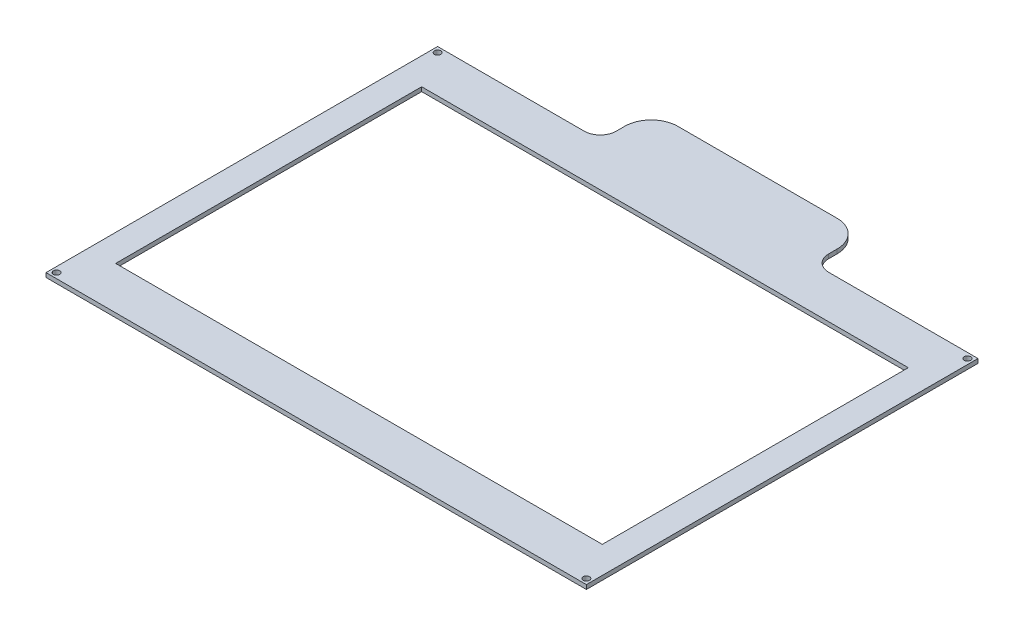
SolidWorks part; units mm, degrees
ref_plane "Front Plane" through (0, 0, 0) normal (0, 0, 1) x (1, 0, 0)
ref_plane "Top Plane" through (0, 0, 0) normal (0, 1, 0) x (1, 0, 0)
ref_plane "Right Plane" through (0, 0, 0) normal (1, 0, 0) x (0, 0, -1)
sketch "Sketch3" plane through (0, 0, 0) normal (0, 1, 0) x (1, 0, 0)
  line L0 (-127.15, 80.1414) -> (-58.1228, 80.1414)
  line L1 (-50.6228, 91.6414) -> (-50.6228, 87.6414)
  line L2 (-38.1228, 104.1414) -> (36.8772, 104.1414)
  line L3 (49.3772, 91.6414) -> (49.3772, 87.6414)
  line L4 (56.8772, 80.1414) -> (127.15, 80.1414)
  line L5 (127.15, 80.1414) -> (127.15, -104.1414)
  line L6 (127.15, -104.1414) -> (-127.15, -104.1414)
  line L7 (-127.15, -104.1414) -> (-127.15, 80.1414)
  line L8 (-114.5, 59.9914) -> (114.5, 59.9914)
  line L9 (-114.5, 59.9914) -> (-114.5, -84.0086)
  line L10 (-114.5, -84.0086) -> (114.5, -84.0086)
  line L11 (114.5, 59.9914) -> (114.5, -84.0086)
  arc A0 (-58.1228, 80.1414) -> (-50.6228, 87.6414) centre (-58.1228, 87.6414) ccw
  arc A1 (-50.6228, 91.6414) -> (-38.1228, 104.1414) centre (-38.1228, 91.6414) cw
  arc A2 (36.8772, 104.1414) -> (49.3772, 91.6414) centre (36.8772, 91.6414) cw
  arc A3 (49.3772, 87.6414) -> (56.8772, 80.1414) centre (56.8772, 87.6414) ccw
  circle A4 centre (-124.6678, 77.6592) radius 1.5
  circle A5 centre (124.6678, 77.6592) radius 1.5
  circle A6 centre (124.6678, -101.6678) radius 1.5
  circle A7 centre (-124.6678, -101.6678) radius 1.5
  point P24 (0, -12.0086)
extrude "Boss-Extrude2" add sketch "Sketch3" along normal blind 2
